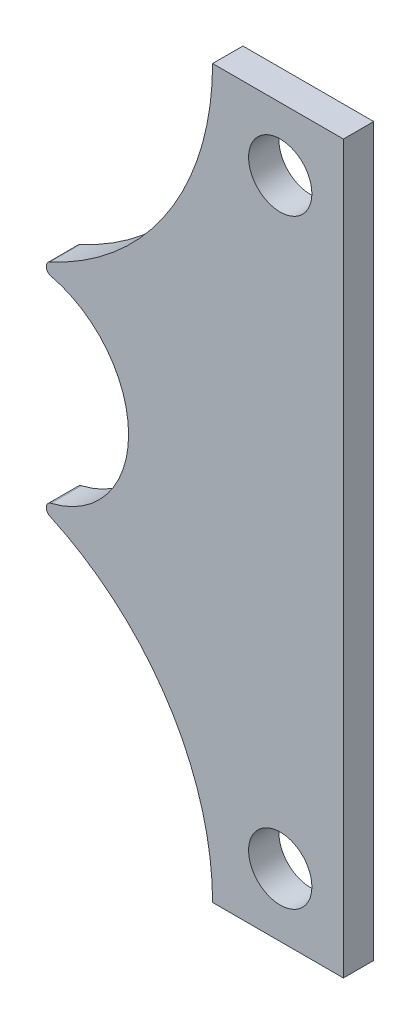
SolidWorks part; units mm, degrees
ref_plane "Front Plane" through (0, 0, 0) normal (0, 0, 1) x (1, 0, 0)
ref_plane "Top Plane" through (0, 0, 0) normal (0, 1, 0) x (1, 0, 0)
ref_plane "Right Plane" through (0, 0, 0) normal (1, 0, 0) x (0, 0, -1)
sketch "Sketch1" plane through (0, 0, 0) normal (0, 0, 1) x (1, 0, 0)
  line L0 (-7.2461, 73.025) -> (-7.2461, -73.025) construction
  line L1 (-19.05, -73.025) -> (19.05, -73.025)
  line L2 (-19.05, -73.025) -> (-19.05, 73.025)
  line L3 (-19.05, 73.025) -> (19.05, 73.025)
  line L4 (19.05, -73.025) -> (19.05, 73.025)
  line L5 (-19.05, -73.025) -> (19.05, 73.025) construction
  line L6 (-19.05, 73.025) -> (19.05, -73.025) construction
  line L7 (-44.45, 20.32) -> (-44.45, -20.32) construction
  line L8 (-44.45, 0) -> (0, 0) construction
  circle A0 centre (-44.45, 0) radius 52.07
  circle A1 centre (6.35, 60.325) radius 6.3627
  circle A2 centre (6.35, -60.325) radius 6.3627
  arc A3 (-7.2461, 73.025) -> (-19.05, 45.4546) centre (-45.3461, 73.025) cw
  circle A4 centre (-44.45, 0) radius 20.32
  arc A5 (-7.2461, 73.025) -> (-44.45, 20.32) centre (-63.1804, 73.025) cw
  arc A6 (-7.2461, -73.025) -> (-44.45, -20.32) centre (-63.1804, -73.025) ccw
  point P0 (0, 0)
  dimension "D2" = 104.14
  dimension "D3" = 12.7254
  dimension "D9" = 38.1
  dimension "D10" = 40.64
  dimension "D1" = 146.05
  dimension "D4" = 12.7
  dimension "D5" = 12.7
  dimension "D6" = 50.8
  dimension "D7" = 38.1
  dimension "D8" = 12.7
extrude "Boss-Extrude1" add sketch "Sketch1" along normal mid plane 6.096 contours A6 L2 A5 A4 | A6 A0 A5 L2 | A6 L1 L4 L3 A5 A0 A2 A1
fillet "Fillet1" radius 1.27 2 edges at (-44.45, -20.32, 0) (-44.45, 20.32, 0)
